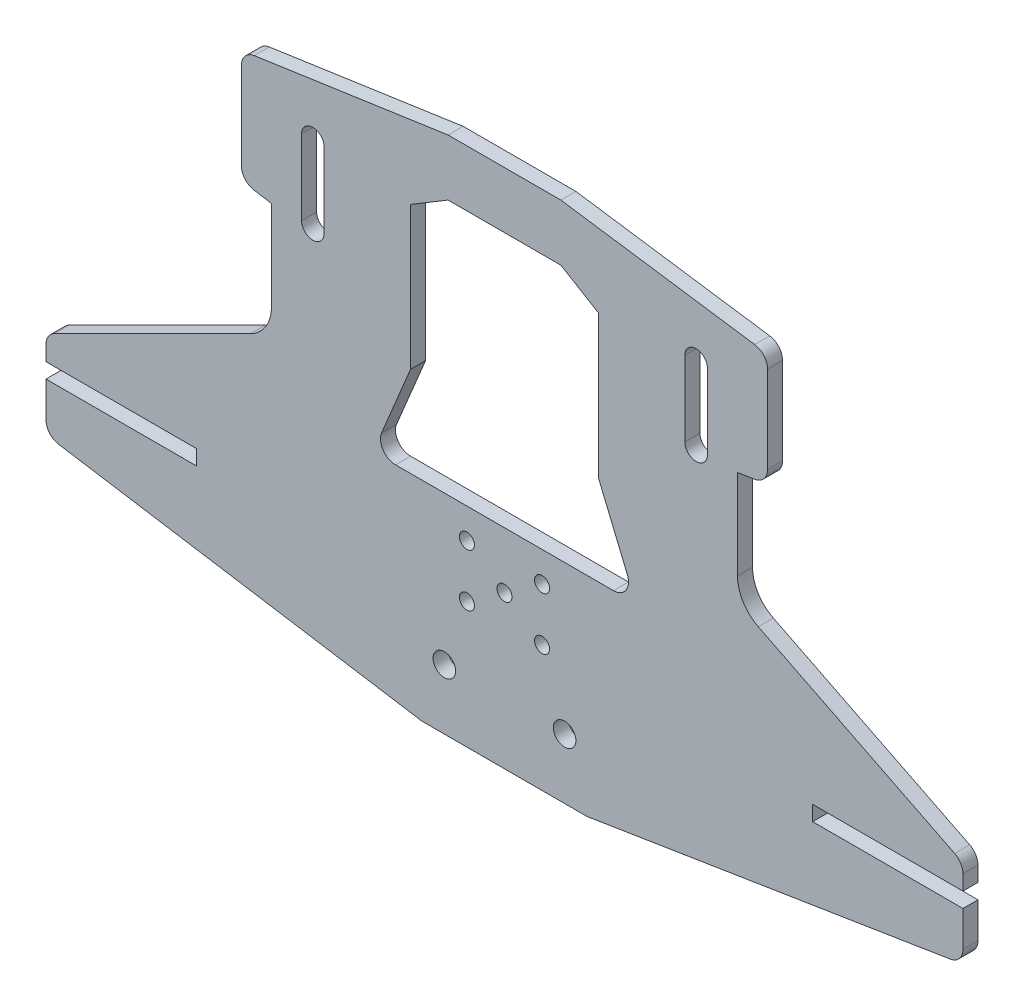
SolidWorks part; units mm, degrees
material "Plástico personalizado"
ref_plane "Plano frontal" through (0, 0, 0) normal (0, 0, 1) x (1, 0, 0)
ref_plane "Plano superior" through (0, 0, 0) normal (0, 1, 0) x (1, 0, 0)
ref_plane "Plano direito" through (0, 0, 0) normal (1, 0, 0) x (0, 0, -1)
sketch "Esboço1" plane through (0, 0, 0) normal (0, 0, 1) x (1, 0, 0)
  line L0 (0, 0) -> (11, 0)
  line L1 (11, 0) -> (59.316, 7.7306)
  line L2 (61, 9.7054) -> (61, 18.404)
  line L3 (59.8944, 20.1928) -> (33.7639, 33.2581)
  line L4 (31, 37.7302) -> (31, 49.6401)
  line L5 (31, 49.6401) -> (33.316, 50.0106)
  line L6 (35, 51.9855) -> (35, 63.5499)
  line L7 (0, 69.2801) -> (7.5, 69.2801)
  line L8 (7.5, 69.2801) -> (33.2879, 65.5291)
  line L9 (0, 61.7801) -> (7.5, 61.7801)
  line L10 (7.5, 61.7801) -> (12.5, 58.7801)
  line L11 (12.5, 58.7801) -> (12.5, 39.7801)
  line L12 (12.5, 39.7801) -> (16.3462, 30.5493)
  line L13 (0, 69.2801) -> (0, 61.7801)
  line L14 (14.5, 27.7801) -> (0, 27.7801)
  line L16 (0, 27.7801) -> (0, 0)
  arc A0 (33.7639, 33.2581) -> (31, 37.7302) centre (36, 37.7302) cw
  arc A1 (59.316, 7.7306) -> (61, 9.7054) centre (59, 9.7054) ccw
  arc A2 (61, 18.404) -> (59.8944, 20.1928) centre (59, 18.404) ccw
  arc A3 (33.2879, 65.5291) -> (35, 63.5499) centre (33, 63.5499) cw
  arc A4 (35, 51.9855) -> (33.316, 50.0106) centre (33, 51.9855) cw
  arc A5 (14.5, 27.7801) -> (16.3462, 30.5493) centre (14.5, 29.7801) ccw
  point P12 (31, 34.6401)
  point P15 (61, 8)
  point P19 (61, 19.6401)
  point P22 (35, 65.2801)
  point P25 (35, 50.2801)
  point P35 (17.5, 27.7801)
  dimension "D11" = 5
  dimension "D12" = 2
  dimension "D19" = 2
  dimension "D1" = 11
  dimension "D2" = 50
  dimension "D3" = 8
  dimension "D4" = 30
  dimension "D5" = 15
  dimension "D6" = 15
  dimension "D7" = 4
  dimension "D8" = 15
  dimension "D9" = 4
  dimension "D10" = 7.5
  dimension "D13" = 7.5
  dimension "D14" = 5
  dimension "D15" = 3
  dimension "D16" = 19
  dimension "D17" = 12
  dimension "D20" = 7.5
extrude "Ressalto-extrusão1" add sketch "Esboço1" along normal blind 2
mirror "Espelhar1" about plane through (0, 0, 0) normal (1, 0, 0) of "Ressalto-extrusão1"
sketch "Esboço2" plane through (0, 0, 2) normal (0, 0, 1) x (1, 0, 0)
  line L0 (-25.5, 59.6619) -> (-25.5, 49.6619) construction
  line L1 (-24, 59.6619) -> (-24, 49.6619)
  line L2 (-27, 59.6619) -> (-27, 49.6619)
  line L3 (-35, 51.9855) -> (-35, 63.5499) construction
  line L4 (0, 73.0397) -> (0, -3.828) construction
  line L5 (25.5, 59.6619) -> (25.5, 49.6619) construction
  line L6 (24, 59.6619) -> (24, 49.6619)
  line L7 (27, 59.6619) -> (27, 49.6619)
  line L8 (-11, 0) -> (11, 0) construction
  line L9 (14.5, 27.7801) -> (-14.5, 27.7801) construction
  line L10 (-61, 9.7054) -> (-61, 18.404) construction
  line L11 (-41, 14.4077) -> (-61, 14.4077)
  line L12 (-41, 14.4077) -> (-41, 16.4077)
  line L13 (-41, 16.4077) -> (-61, 16.4077)
  line L14 (-61, 16.4077) -> (-61, 14.4077)
  line L15 (61, 16.4077) -> (61, 14.4077)
  line L16 (41, 16.4077) -> (61, 16.4077)
  line L17 (41, 14.4077) -> (41, 16.4077)
  line L18 (41, 14.4077) -> (61, 14.4077)
  arc A0 (-24, 59.6619) -> (-27, 59.6619) centre (-25.5, 59.6619) ccw
  arc A1 (-27, 49.6619) -> (-24, 49.6619) centre (-25.5, 49.6619) ccw
  arc A2 (24, 59.6619) -> (27, 59.6619) centre (25.5, 59.6619) cw
  arc A3 (27, 49.6619) -> (24, 49.6619) centre (25.5, 49.6619) cw
  circle A4 centre (-5, 23.7801) radius 1
  circle A5 centre (5, 23.7801) radius 1
  circle A6 centre (5, 16.7801) radius 1
  circle A7 centre (-5, 16.7801) radius 1
  circle A8 centre (0, 20.2801) radius 1
  circle A9 centre (-8, 8) radius 1.5
  circle A10 centre (8, 8) radius 1.5
  arc A11 (-61, 9.7054) -> (-59.316, 7.7306) centre (-59, 9.7054) ccw construction
  point P2 (-25.5, 54.6619)
  point P13 (25.5, 54.6619)
  point P37 (-51, 15.4077)
  point P44 (-60.5218, 8.4077)
  point P52 (51, 15.4077)
  dimension "D1" = 10
  dimension "D4" = 2
  dimension "D8" = 3
  dimension "D2" = 3
  dimension "D3" = 8
  dimension "D5" = 10
  dimension "D6" = 5
  dimension "D7" = 7
  dimension "D9" = 8
  dimension "D10" = 4
  dimension "D11" = 3.5
  dimension "D12" = 16
  dimension "D13" = 8
  dimension "D14" = 20
  dimension "D15" = 2
  dimension "D16" = 6
extrude "Corte-extrusão1" cut sketch "Esboço2" against normal through all
